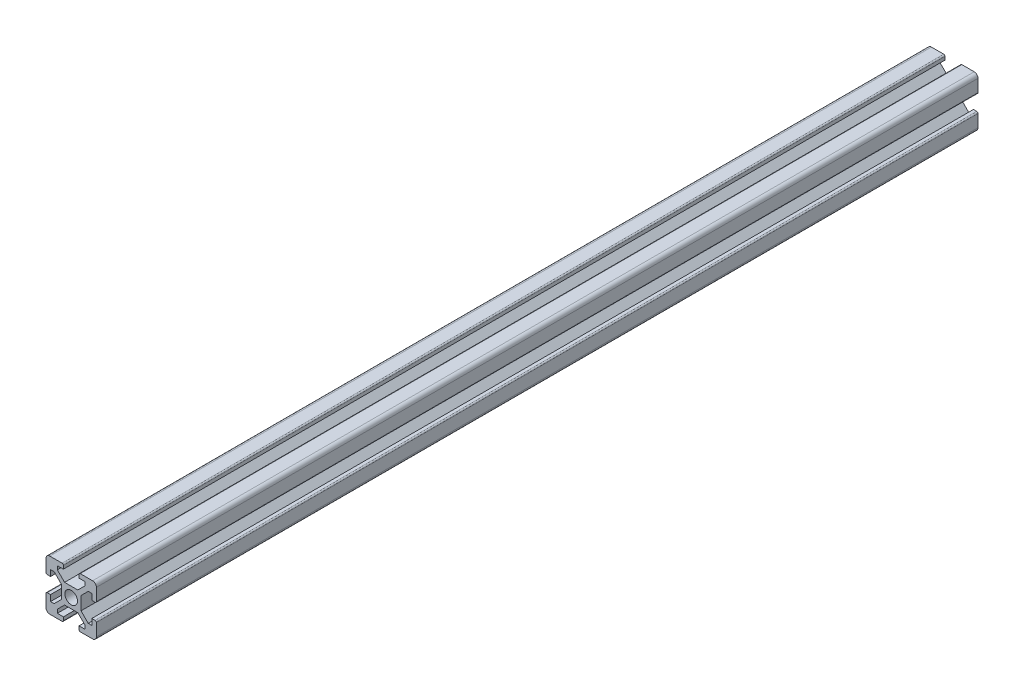
SolidWorks part; units mm, degrees
ref_plane "前视基准面" through (0, 0, 0) normal (0, 0, 1) x (1, 0, 0)
ref_plane "上视基准面" through (0, 0, 0) normal (0, 1, 0) x (1, 0, 0)
ref_plane "右视基准面" through (0, 0, 0) normal (1, 0, 0) x (0, 0, -1)
sketch "草图1" plane through (0, 0, 0) normal (0, 0, 1) x (1, 0, 0)
  line L0 (0, 6.9) -> (0, 0)
  line L1 (20, 20) -> (20, 13.1)
  line L2 (1.8, 15.5) -> (3.2272, 15.5)
  line L3 (4.5, 16.7728) -> (4.5, 18.2)
  line L4 (0, 13.1) -> (0, 20)
  line L5 (6.9, 20) -> (6.9, 18.2)
  line L6 (6.9, 18.2) -> (4.5, 18.2)
  line L7 (13.1, 20) -> (20, 20)
  line L8 (6.9, 20) -> (0, 20)
  line L9 (0, 0) -> (6.9, 0)
  line L10 (13.1, 0) -> (20, 0)
  line L11 (15.5, 18.2) -> (15.5, 16.7728)
  line L12 (16.7728, 15.5) -> (18.2, 15.5)
  line L13 (20, 6.9) -> (20, 0)
  line L14 (1.8, 4.5) -> (3.2272, 4.5)
  line L15 (4.5, 3.2272) -> (4.5, 1.8)
  line L16 (12.6272, 6.1) -> (15.5, 3.2272)
  line L17 (18.2, 4.5) -> (16.7728, 4.5)
  line L18 (15.5, 3.2272) -> (15.5, 1.8)
  line L19 (13.9, 7.3728) -> (16.7728, 4.5)
  line L20 (13.1, 20) -> (13.1, 18.2)
  line L21 (13.1, 18.2) -> (15.5, 18.2)
  line L22 (7.3728, 13.9) -> (12.6272, 13.9)
  line L23 (13.9, 12.6272) -> (13.9, 7.3728)
  line L24 (7.3728, 6.1) -> (12.6272, 6.1)
  line L25 (6.1, 12.6272) -> (6.1, 7.3728)
  line L27 (12.6272, 13.9) -> (15.5, 16.7728)
  line L30 (3.2272, 4.5) -> (6.1, 7.3728)
  line L32 (4.5, 3.2272) -> (7.3728, 6.1)
  line L33 (20, 13.1) -> (18.2, 13.1)
  line L34 (18.2, 13.1) -> (18.2, 15.5)
  line L36 (20, 6.9) -> (18.2, 6.9)
  line L37 (18.2, 6.9) -> (18.2, 4.5)
  line L39 (13.1, 0) -> (13.1, 1.8)
  line L40 (13.1, 1.8) -> (15.5, 1.8)
  line L42 (6.9, 0) -> (6.9, 1.8)
  line L43 (6.9, 1.8) -> (4.5, 1.8)
  line L45 (0, 6.9) -> (1.8, 6.9)
  line L46 (1.8, 6.9) -> (1.8, 4.5)
  line L48 (0, 13.1) -> (1.8, 13.1)
  line L49 (1.8, 13.1) -> (1.8, 15.5)
  line L50 (4.5, 16.7728) -> (7.3728, 13.9)
  line L51 (3.2272, 15.5) -> (6.1, 12.6272)
  line L53 (13.9, 12.6272) -> (16.7728, 15.5)
  line L62 (1.8, 13.1) -> (1.8, 15.5)
  line L63 (0, 13.1) -> (1.8, 13.1)
  line L66 (6.9, 18.2) -> (4.5, 18.2)
  line L67 (6.9, 20) -> (6.9, 18.2)
  line L68 (3.2272, 15.5) -> (1.8, 15.5)
  line L69 (4.5, 18.2) -> (4.5, 16.7728)
  line L75 (4.5, 1.8) -> (4.5, 3.2272)
  line L76 (3.2272, 4.5) -> (1.8, 4.5)
  line L77 (6.9, 0) -> (6.9, 1.8)
  line L78 (6.9, 1.8) -> (4.5, 1.8)
  line L80 (0, 6.9) -> (1.8, 6.9)
  line L81 (1.8, 6.9) -> (1.8, 4.5)
  line L90 (1.8, 6.9) -> (1.8, 4.5)
  line L91 (0, 6.9) -> (1.8, 6.9)
  line L93 (18.2, 6.9) -> (18.2, 4.5)
  line L94 (20, 6.9) -> (18.2, 6.9)
  line L98 (13.1, 1.8) -> (15.5, 1.8)
  line L99 (13.1, 0) -> (13.1, 1.8)
  line L100 (16.7728, 4.5) -> (18.2, 4.5)
  line L101 (15.5, 1.8) -> (15.5, 3.2272)
  line L106 (6.9, 1.8) -> (4.5, 1.8)
  line L107 (6.9, 0) -> (6.9, 1.8)
  line L109 (4.5, 3.2272) -> (4.5, 1.8)
  line L110 (1.8, 4.5) -> (3.2272, 4.5)
  circle A0 centre (10, 10) radius 2.5
extrude "凸台-拉伸1" add sketch "草图1" along normal blind 350 contours L23 L53 L12 L34 L33 L1 L7 L20 L21 L11 L27 L22 L50 L3 L6 L5 L8 L4 L48 L49 L2 L51 L25 L30 L14 L46 L45 L0 L9 L42 L43 L15 L32 L24 L16 L18 L40 L39 L10 L13 L36 L37 L17 L19
fillet "圆角1" radius 1.5 1 edges at (20, 20, 175)
fillet "圆角2" radius 1.5 1 edges at (0, 20, 175)
fillet "圆角3" radius 1.5 1 edges at (0, 0, 175)
fillet "圆角4" radius 1.5 1 edges at (20, 0, 175)
fillet "圆角5" radius 0.5 1 edges at (13.1, 20, 175)
fillet "圆角6" radius 0.5 1 edges at (6.9, 20, 175)
fillet "圆角7" radius 0.5 1 edges at (0, 13.1, 175)
fillet "圆角8" radius 0.5 1 edges at (0, 6.9, 175)
fillet "圆角9" radius 0.5 1 edges at (6.9, 0, 175)
fillet "圆角10" radius 0.5 1 edges at (13.1, 0, 175)
fillet "圆角11" radius 0.5 1 edges at (20, 13.1, 175)
fillet "圆角12" radius 0.5 1 edges at (20, 6.9, 175)
